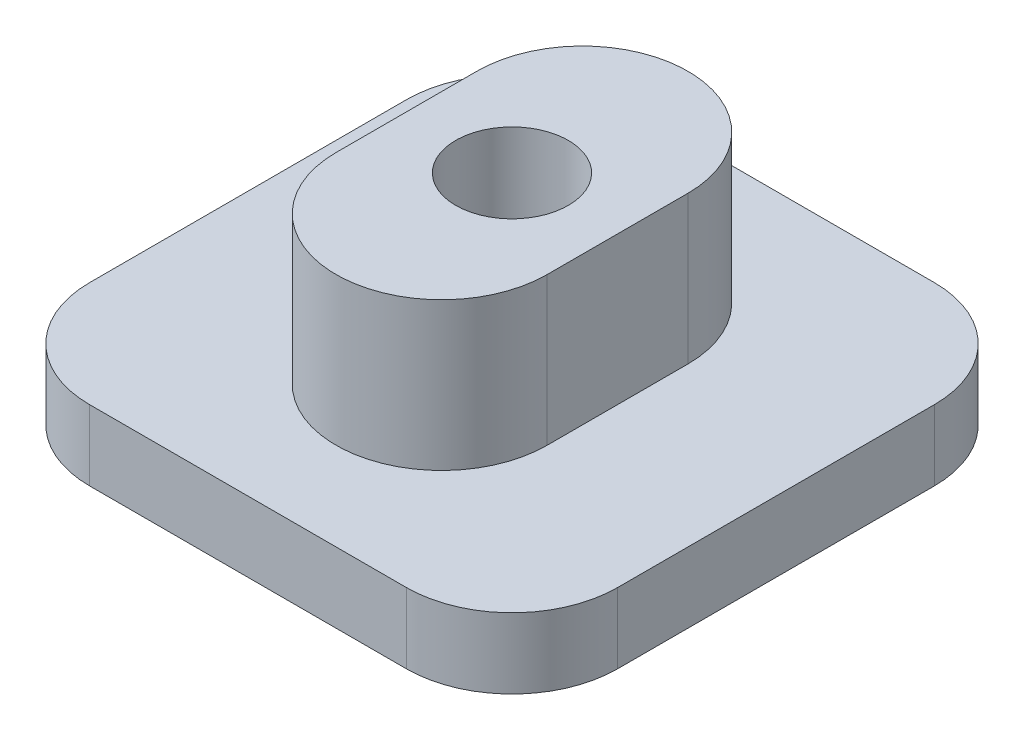
SolidWorks part; units mm, degrees
ref_plane "Front Plane" through (0, 0, 0) normal (0, 0, 1) x (1, 0, 0)
ref_plane "Top Plane" through (0, 0, 0) normal (0, 1, 0) x (1, 0, 0)
ref_plane "Right Plane" through (0, 0, 0) normal (1, 0, 0) x (0, 0, -1)
sketch "Sketch1" plane through (0, 0, 0) normal (0, 1, 0) x (1, 0, 0)
  line L0 (0, -2) -> (0, 2) construction
  line L1 (-3, -2) -> (-3, 2)
  line L2 (3, -2) -> (3, 2)
  arc A0 (-3, -2) -> (3, -2) centre (0, -2) ccw
  arc A1 (3, 2) -> (-3, 2) centre (0, 2) ccw
  circle A2 centre (0, 0) radius 1.6
  point P2 (0, 0)
  dimension "D2" = 3
  dimension "D3" = 3.2
  dimension "D1" = 4
extrude "Boss-Extrude1" add sketch "Sketch1" along normal blind 4.2
sketch "Sketch2" plane through (0, 0, 0) normal (0, -1, 0) x (1, 0, 0)
  line L1 (7.5, 7.5) -> (-7.5, 7.5)
  line L2 (7.5, 7.5) -> (7.5, -7.5)
  line L3 (7.5, -7.5) -> (-7.5, -7.5)
  line L4 (-7.5, 7.5) -> (-7.5, -7.5)
  line L5 (0, -7.5) -> (0, 7.5) construction
  line L6 (7.5, 0) -> (-7.5, 0) construction
  point P0 (0, 0)
  dimension "D1" = 15
  dimension "D2" = 15
extrude "Boss-Extrude2" add sketch "Sketch2" along normal blind 2
fillet "Fillet1" radius 3 4 edges at (7.5, -1, -7.5) (-7.5, -1, -7.5) (-7.5, -1, 7.5) (7.5, -1, 7.5)
sketch "Sketch3" plane through (0, 0, 0) normal (0, 1, 0) x (1, 0, 0)
  circle A0 centre (0, 0) radius 1.6
  dimension "D1" = 3.2
extrude "Cut-Extrude1" cut sketch "Sketch3" against normal through all both and the other way through all
